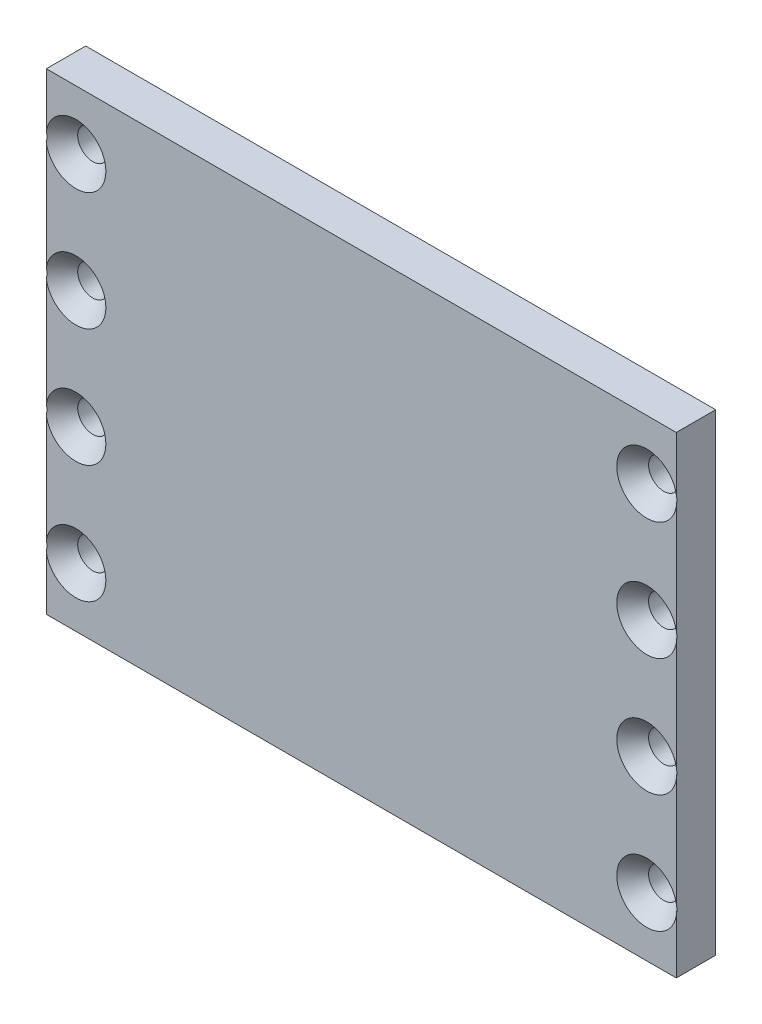
SolidWorks part; units mm, degrees
ref_plane "Front Plane" through (0, 0, 0) normal (0, 0, 1) x (1, 0, 0)
ref_plane "Top Plane" through (0, 0, 0) normal (0, 1, 0) x (1, 0, 0)
ref_plane "Right Plane" through (0, 0, 0) normal (1, 0, 0) x (0, 0, -1)
sketch "Sketch1" plane through (0, 0, 0) normal (0, 0, 1) x (1, 0, 0)
  line L1 (-101.6, 76.2) -> (101.6, 76.2)
  line L2 (-101.6, 76.2) -> (-101.6, -76.2)
  line L3 (-101.6, -76.2) -> (101.6, -76.2)
  line L4 (101.6, 76.2) -> (101.6, -76.2)
  line L5 (-101.6, 76.2) -> (101.6, -76.2) construction
  line L6 (-101.6, -76.2) -> (101.6, 76.2) construction
  point P0 (0, 0)
  dimension "D1" = 203.2
  dimension "D2" = 152.4
extrude "Boss-Extrude1" add sketch "Sketch1" along normal blind 12.7
hole_wizard "CSK for 3/8 Flat Head Machine Screw1" positions "Sketch3" profile "Sketch2" countersink size "3/8" standard "ANSI Inch" end condition through all
sketch "Sketch3" plane through (0, 0, 12.7) normal (0, 0, 1) x (1, 0, 0)
  line L0 (92.075, 57.15) -> (92.075, -57.15) construction
  line L1 (-92.075, 57.15) -> (-92.075, -57.15) construction
  line L2 (-92.075, 0) -> (92.075, 0) construction
  point P0 (-92.075, 57.15)
  point P4 (-92.075, -57.15)
  point P6 (92.075, -57.15)
  point P10 (92.075, 57.15)
  point P24 (-92.075, 19.05)
  point P26 (92.075, 19.05)
  point P28 (92.075, -19.05)
  point P30 (-92.075, -19.05)
  dimension "D1" = 114.3
  dimension "D2" = 114.3
  dimension "D3" = 184.15
  dimension "D4" = 38.1
  dimension "D5" = 38.1
  dimension "D6" = 38.1
  dimension "D7" = 38.1
sketch "Sketch2" plane through (-92.075, 57.15, 12.7) normal (1, 0, 0) x (0, -1, 0)
  line L0 (0, 0) -> (0, 12.7)
  line L1 (0, 12.7) -> (4.9022, 12.7)
  line L2 (4.9022, 12.7) -> (4.9022, 5.4932)
  line L3 (4.9022, 5.4932) -> (9.6774, 0)
  line L5 (9.6774, 0) -> (0, 0)
  line L6 (-4.9022, 5.4932) -> (-9.6774, 0) construction
  line L11 (0, -6.35) -> (0, 107.95) construction
  dimension "Thru Hole Dia." = 9.8044
  dimension "Thru Hole Depth" = 12.7
  dimension "Near C'Sink Dia." = 19.3548
  dimension "Near C'Sink Angle" = 82
sketch "Sketch4" plane through (0, 0, 0) normal (0, 0, -1) x (-1, 0, 0)
  line L0 (0, 76.2) -> (0, -76.2) construction
  line L1 (-101.6, 76.2) -> (101.6, 76.2) construction
  line L2 (101.6, -76.2) -> (-101.6, -76.2) construction
sketch "Sketch5" plane through (0, 0, 12.7) normal (0, 0, 1) x (1, 0, 0)
  line L0 (0, 76.2) -> (0, -76.2) construction
  line L1 (101.6, 76.2) -> (-101.6, 76.2) construction
  line L2 (-101.6, -76.2) -> (101.6, -76.2) construction
